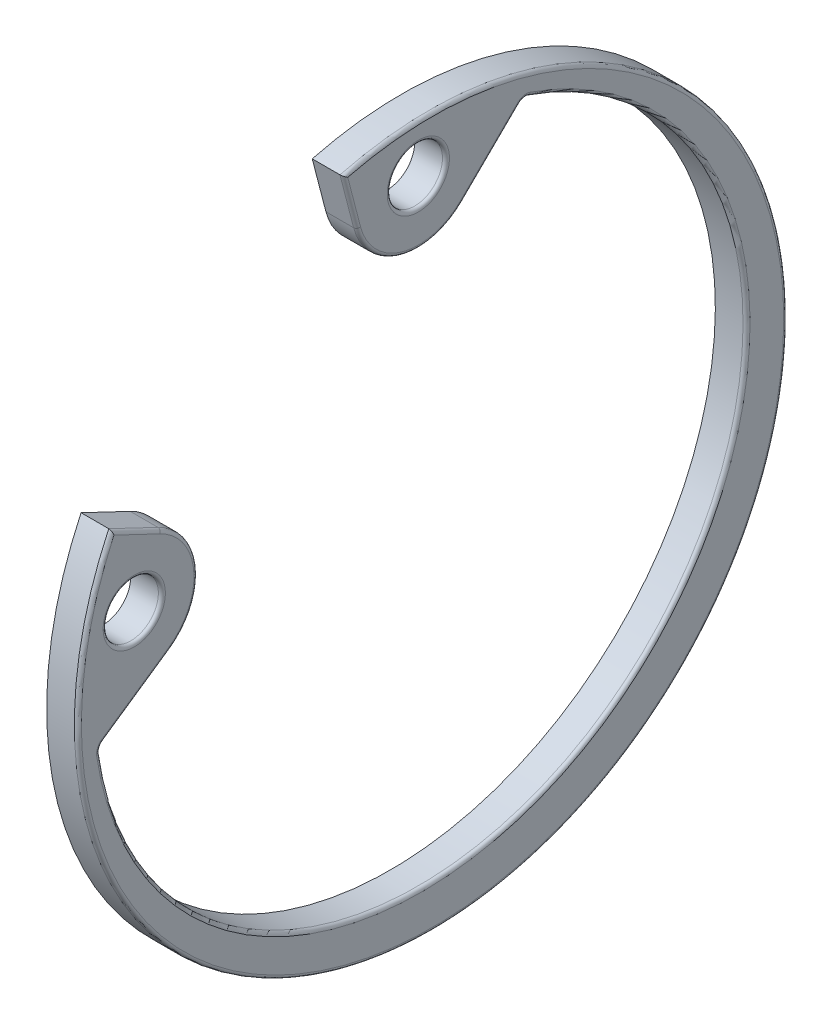
SolidWorks part; units mm, degrees
material "AISI 1020"
ref_plane "Front Plane" through (0, 0, 0) normal (0, 0, 1) x (1, 0, 0)
ref_plane "Top Plane" through (0, 0, 0) normal (0, 1, 0) x (1, 0, 0)
ref_plane "Right Plane" through (0, 0, 0) normal (1, 0, 0) x (0, 0, -1)
sketch "Sketch1" plane through (0, 0, 0) normal (1, 0, 0) x (0, 0, -1)
  line B0 (-9.3728, -0.7352) -> (-7.4838, 0.5656)
  line B1 (-7.7316, 3.6793) -> (-9.134, 4.3467)
  line B2 (-2.5414, 9.7911) -> (-2.1512, 8.2878)
  line B3 (0.8595, 7.4557) -> (2.494, 9.0648)
  circle B4 centre (-8.5066, 2.0509) radius 0.7874
  circle B5 centre (-0.4057, 8.7409) radius 0.7874
  arc B6 (-7.4838, 0.5656) -> (-7.7316, 3.6793) centre (-8.5066, 2.0509) ccw
  arc B7 (-9.134, 4.3467) -> (-2.5414, 9.7911) centre (0, 0) ccw
  arc B8 (-2.1512, 8.2878) -> (0.8595, 7.4557) centre (-0.4057, 8.7409) ccw
  arc B9 (2.7563, 9.1235) -> (2.494, 9.0648) centre (2.6721, 8.8838) ccw
  arc B10 (-9.48, -0.9817) -> (2.7563, 9.1235) centre (-0.3131, 0.3791) ccw
  arc B11 (-9.3728, -0.7352) -> (-9.48, -0.9817) centre (-9.2288, -0.9444) ccw
sketch_block_instance "Block-circlip block-1"
sketch_block "Block-circlip block"
extrude "Boss-Extrude1" add sketch "Sketch1" along normal blind 0.89
fillet "Fillet1" radius 0.1 12 edges at (0.89, 8.7409, -0.3817) (0.89, -6.7666, -5.5881) (0.89, 9.1317, -2.6167) (0.89, 8.2603, -1.6767) (0.89, 7.0027, 0.8861) (0.89, 9.0394, 2.3463) (0.89, -7.7997, -6.4412) (0.89, 4.013, 8.4328) (0.89, 2.194, 6.7088) (0.89, -0.0848, 8.4283) (0.89, -0.8431, 9.4617) (0.89, 2.0509, 7.7192)
